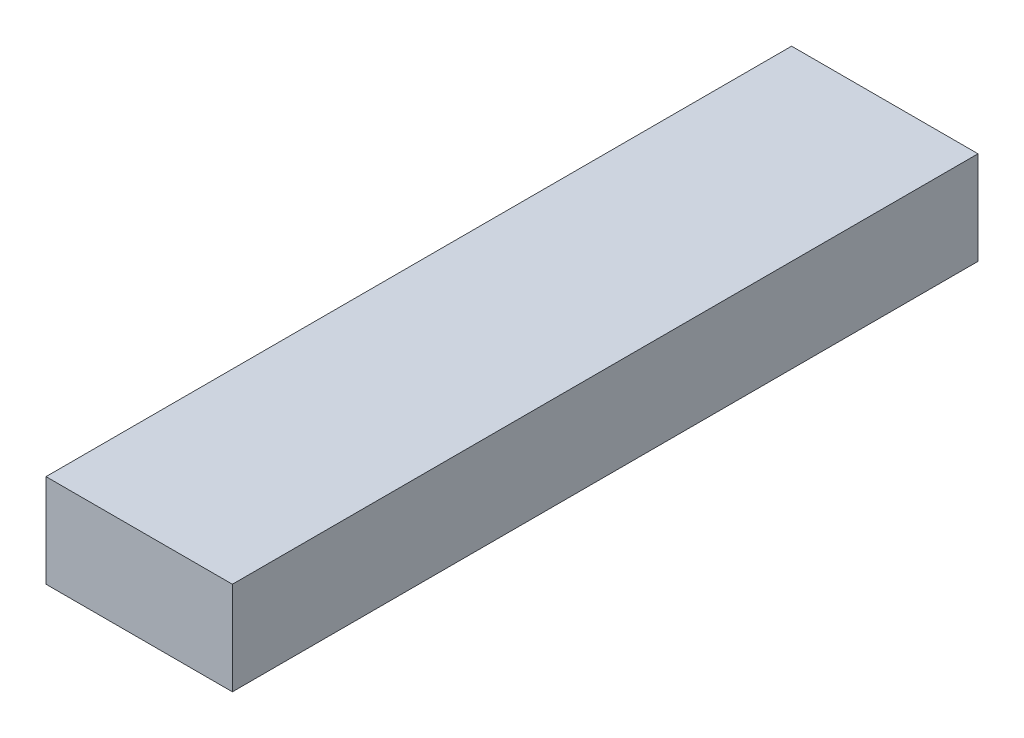
SolidWorks part; units mm, degrees
ref_plane "Front Plane" through (0, 0, 0) normal (0, 0, 1) x (1, 0, 0)
ref_plane "Top Plane" through (0, 0, 0) normal (0, 1, 0) x (1, 0, 0)
ref_plane "Right Plane" through (0, 0, 0) normal (1, 0, 0) x (0, 0, -1)
sketch "Sketch1" plane through (0, 0, 0) normal (0, 0, 1) x (1, 0, 0)
  line L1 (-5, -2.5) -> (5, -2.5)
  line L2 (-5, -2.5) -> (-5, 2.5)
  line L3 (-5, 2.5) -> (5, 2.5)
  line L4 (5, -2.5) -> (5, 2.5)
  line L5 (-5, -2.5) -> (5, 2.5) construction
  line L6 (-5, 2.5) -> (5, -2.5) construction
  point P0 (0, 0)
  dimension "D1" = 5
  dimension "D2" = 10
extrude "Boss-Extrude1" add sketch "Sketch1" along normal blind 40
